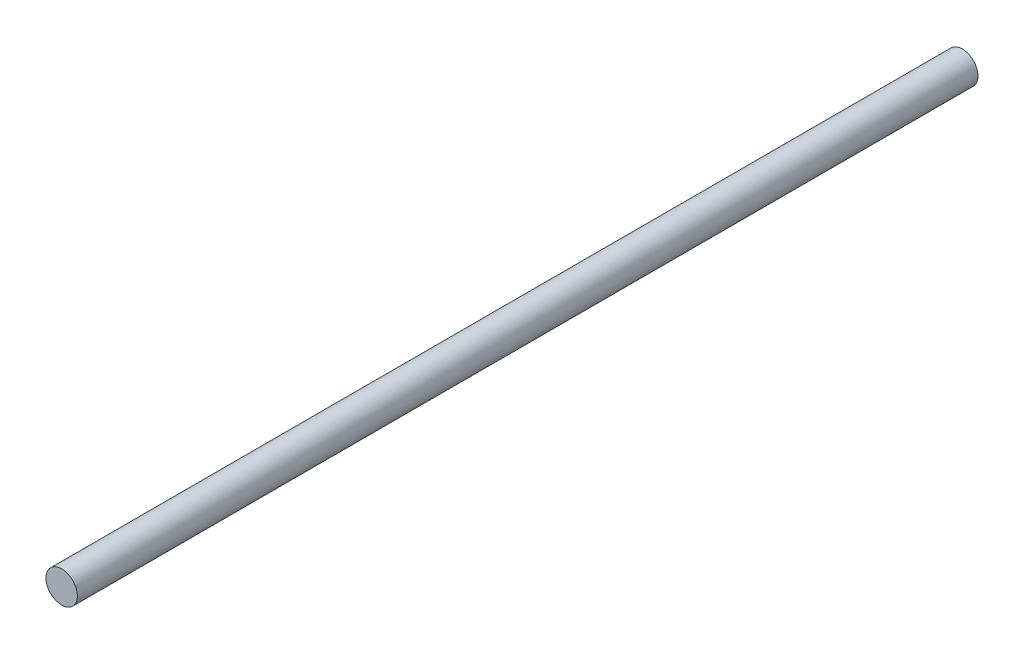
SolidWorks part; units mm, degrees
ref_plane "Plan de face" through (0, 0, 0) normal (0, 0, 1) x (1, 0, 0)
ref_plane "Plan de dessus" through (0, 0, 0) normal (0, 1, 0) x (1, 0, 0)
ref_plane "Plan de droite" through (0, 0, 0) normal (1, 0, 0) x (0, 0, -1)
sketch "Sketch1" plane through (0, 0, 0) normal (0, 0, 1) x (1, 0, 0)
  circle A0 centre (0, 0) radius 5
  dimension "D1" = 10
extrude "Boss-Extrude1" add sketch "Sketch1" along normal blind 286.9
